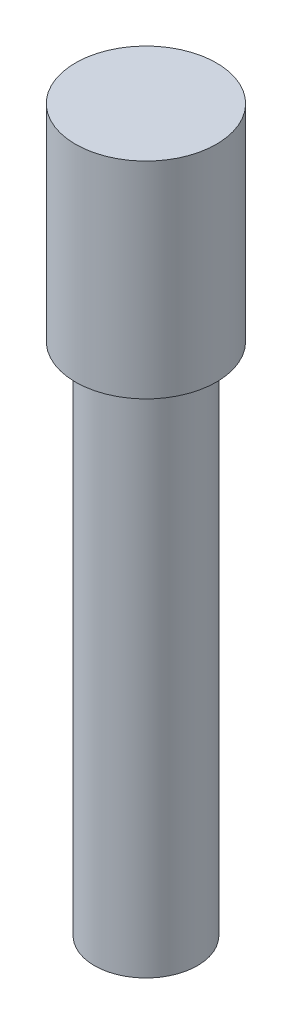
SolidWorks part; units mm, degrees
ref_plane "Front Plane" through (0, 0, 0) normal (0, 0, 1) x (1, 0, 0)
ref_plane "Top Plane" through (0, 0, 0) normal (0, 1, 0) x (1, 0, 0)
ref_plane "Right Plane" through (0, 0, 0) normal (1, 0, 0) x (0, 0, -1)
sketch "Sketch1" plane through (0, 0, 0) normal (0, 1, 0) x (1, 0, 0)
  circle A0 centre (0, 0) radius 0.5
  dimension "D1" = 1
extrude "Boss-Extrude1" add sketch "Sketch1" along normal blind 5
sketch "Sketch2" plane through (0, 5, 0) normal (0, 1, 0) x (1, 0, 0)
  circle A0 centre (0, 0) radius 0.6845
extrude "Boss-Extrude2" add sketch "Sketch2" along normal blind 2
